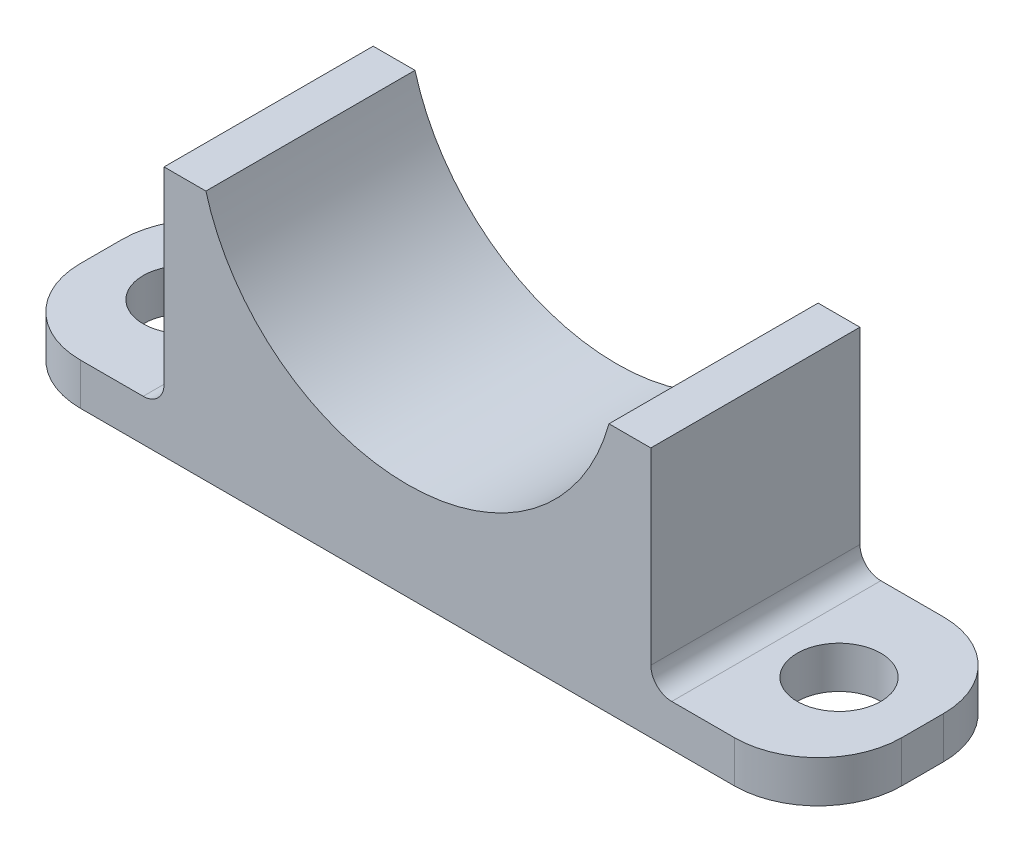
SolidWorks part; units mm, degrees
ref_plane "Plano frontal" through (0, 0, 0) normal (0, 0, 1) x (1, 0, 0)
ref_plane "Plano superior" through (0, 0, 0) normal (0, 1, 0) x (1, 0, 0)
ref_plane "Plano direito" through (0, 0, 0) normal (1, 0, 0) x (0, 0, -1)
sketch "Esboço2" plane through (0, 0, 0) normal (0, 0, 1) x (1, 0, 0)
  line L0 (24.0976, -6.6563) -> (29.0976, -6.6563)
  line L1 (29.0976, -6.6563) -> (29.0976, -36.6563)
  line L2 (29.0976, -36.6563) -> (-29.0976, -36.6563)
  line L3 (-29.0976, -36.6563) -> (-29.0976, -6.6563)
  line L4 (-29.0976, -6.6563) -> (-24.0976, -6.6563)
  line L5 (0, 12.9872) -> (0, -42.4637) construction
  line L6 (-42.7534, 0) -> (45.5812, 0) construction
  arc A0 (-24.0976, -6.6563) -> (24.0976, -6.6563) centre (0, 0) ccw
  dimension "D1" = 25
  dimension "D2" = 5
  dimension "D3" = 5
  dimension "D4" = 30
extrude "Ressalto-extrusão1" add sketch "Esboço2" along normal blind 25
sketch "Esboço3" plane through (-29.0976, 0, 0) normal (-1, 0, 0) x (0, 0, 1)
  line L0 (25, -6.6563) -> (25, -36.6563) construction
  line L1 (0, -36.6563) -> (25, -36.6563)
  line L2 (0, -36.6563) -> (0, -31.6563)
  line L3 (0, -31.6563) -> (25, -31.6563)
  line L4 (25, -36.6563) -> (25, -31.6563)
  dimension "D1" = 5
extrude "Ressalto-extrusão2" add sketch "Esboço3" along normal blind 20
fillet "Filete1" radius 10 1 edges at (-49.0976, -34.1563, 25)
fillet "Filete2" radius 10 1 edges at (-49.0976, -34.1563, 0)
sketch "Esboço4" plane through (29.0976, 0, 0) normal (1, 0, 0) x (0, 0, -1)
  line L0 (0, -36.6563) -> (0, -6.6563) construction
  line L1 (-25, -36.6563) -> (0, -36.6563)
  line L2 (-25, -36.6563) -> (-25, -31.6563)
  line L3 (-25, -31.6563) -> (0, -31.6563)
  line L4 (0, -36.6563) -> (0, -31.6563)
  dimension "D1" = 5
extrude "Ressalto-extrusão3" add sketch "Esboço4" along normal blind 20
fillet "Filete3" radius 10 1 edges at (49.0976, -34.1563, 25)
fillet "Filete4" radius 10 1 edges at (49.0976, -34.1563, 0)
sketch "Esboço5" plane through (0, -31.6563, 0) normal (0, 1, 0) x (1, 0, 0)
  line L0 (39.0976, 0) -> (29.0976, 0) construction
  line L1 (49.0976, -10) -> (49.0976, -15) construction
  line L2 (0, 13.2727) -> (0, -31.5735) construction
  circle A0 centre (39.0976, -12.5) radius 5
  circle A1 centre (-39.0976, -12.5) radius 5
  dimension "D1" = 10
  dimension "D2" = 12.5
  dimension "D3" = 10
extrude "Corte-extrusão1" cut sketch "Esboço5" against normal blind 20
fillet "Filete5" radius 2.5 1 edges at (-29.0976, -31.6563, 12.5)
fillet "Filete6" radius 2.5 1 edges at (29.0976, -31.6563, 12.5)
